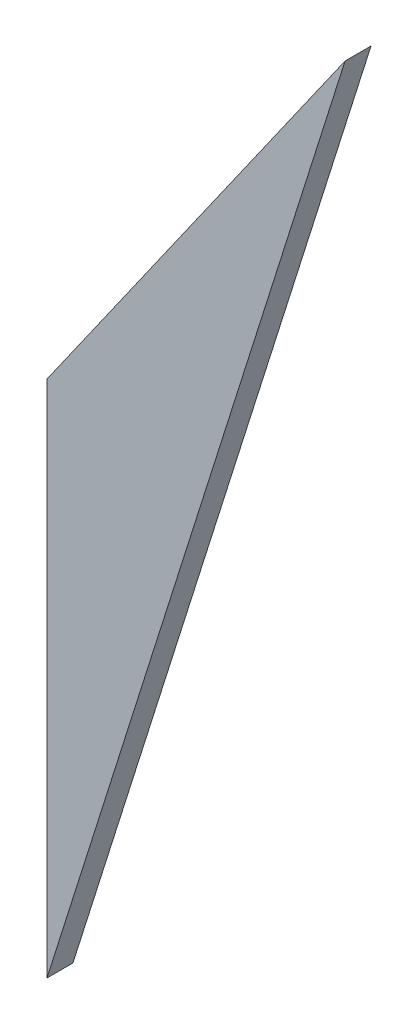
SolidWorks part; units mm, degrees
ref_plane "Plan de face" through (0, 0, 0) normal (0, 0, 1) x (1, 0, 0)
ref_plane "Plan de dessus" through (0, 0, 0) normal (0, 1, 0) x (1, 0, 0)
ref_plane "Plan de droite" through (0, 0, 0) normal (1, 0, 0) x (0, 0, -1)
sketch "Esquisse1" plane through (0, 0, 0) normal (0, 0, 1) x (1, 0, 0)
  line L0 (-195.5174, 119.1533) -> (-230, 70.0518)
  line L1 (-230, 70.0518) -> (-230, 10.0518)
  line L2 (-230, 10.0518) -> (-195.5174, 119.1533)
  line L3 (-186.6629, 131.7617) -> (-230.5449, 69.2759) construction
  line L4 (-230, -9) -> (-230, 71) construction
  dimension "D1" = 60
  dimension "D2" = 60
extrude "Boss.-Extru.1" add sketch "Esquisse1" against normal blind 3
